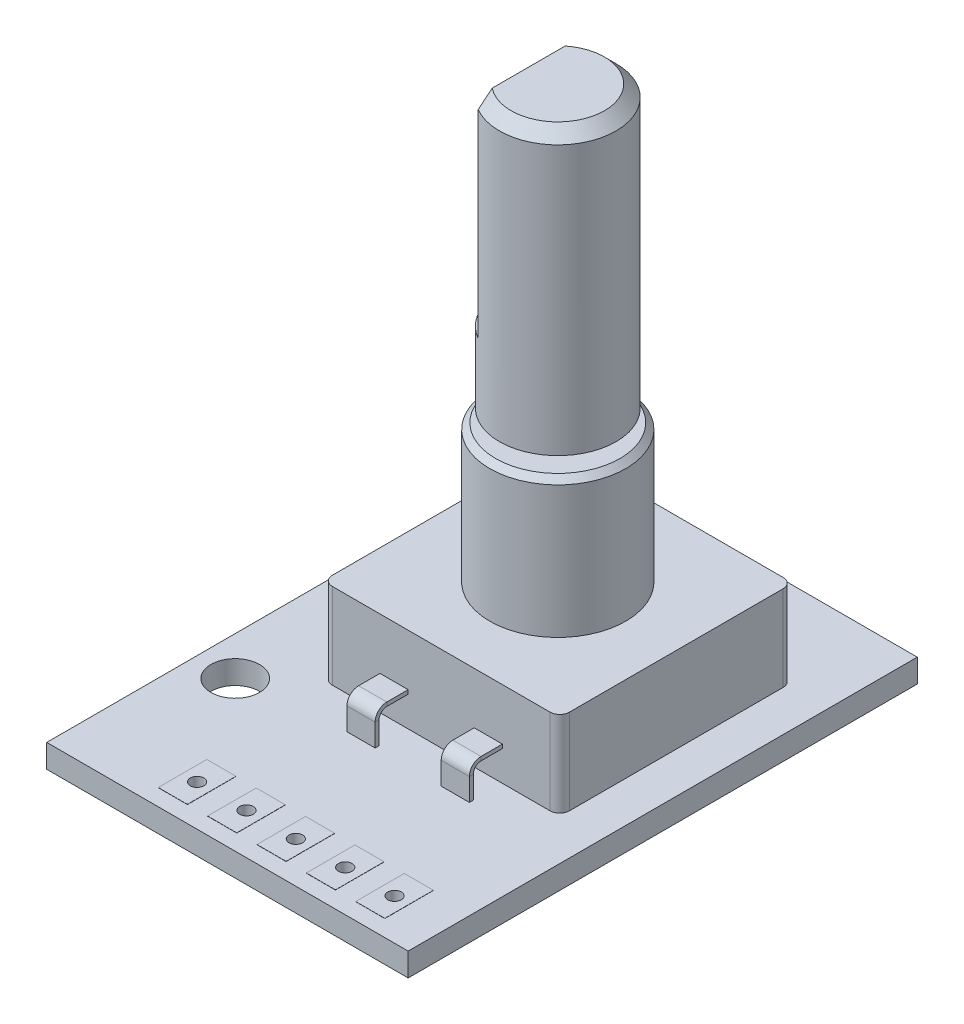
SolidWorks part; units mm, degrees
ref_plane "Front Plane" through (0, 0, 0) normal (0, 0, 1) x (1, 0, 0)
ref_plane "Top Plane" through (0, 0, 0) normal (0, 1, 0) x (1, 0, 0)
ref_plane "Right Plane" through (0, 0, 0) normal (1, 0, 0) x (0, 0, -1)
sketch "Sketch1" plane through (0, 0, 0) normal (0, 1, 0) x (1, 0, 0)
  line L0 (-7.3, 8.3) -> (-7.3, -5.4) construction
  line L1 (-9.3, 13.1) -> (9.3, 13.1)
  line L2 (-9.3, 13.1) -> (-9.3, -13.1)
  line L3 (-9.3, -13.1) -> (9.3, -13.1)
  line L4 (9.3, 13.1) -> (9.3, -13.1)
  line L5 (-9.3, 13.1) -> (9.3, -13.1) construction
  line L6 (-9.3, -13.1) -> (9.3, 13.1) construction
  circle A0 centre (-7.3, 8.3) radius 1.25
  circle A1 centre (-7.3, -5.4) radius 1.25
  point P0 (0, 0)
  point P11 (0, 0)
  point P12 (0, 0)
  point P13 (-6.0699, 9.8258)
  dimension "D3" = 2.5
  dimension "D1" = 18.6
  dimension "D2" = 26.2
  dimension "D4" = 13.7
  dimension "D5" = 4.8
  dimension "D6" = 2
extrude "Boss-Extrude1" add sketch "Sketch1" along normal blind 1.2
sketch "Sketch3" plane through (0, 1.2, 0) normal (0, 1, 0) x (1, 0, 0)
  line L0 (9.3, -13.1) -> (9.3, 13.1) construction
  line L1 (-5, -3.2) -> (7.2, -3.2)
  line L2 (-5, -3.2) -> (-5, 8.8)
  line L3 (-5, 8.8) -> (7.2, 8.8)
  line L4 (7.2, -3.2) -> (7.2, 8.8)
  line L5 (-5, -3.2) -> (7.2, 8.8) construction
  line L6 (-5, 8.8) -> (7.2, -3.2) construction
  line L7 (9.3, 13.1) -> (-9.3, 13.1) construction
  point P0 (1.1, 2.8)
  dimension "D1" = 12
  dimension "D2" = 12.2
  dimension "D3" = 2.1
  dimension "D4" = 4.3
extrude "Boss-Extrude2" add sketch "Sketch3" along normal blind 4.4
sketch3d "3DSketch5"
  line L0 (1.1, 5.6, 3.2) -> (1.1, 1.2, 3.2) construction
  line L7 (-5, 5.6, 3.2) -> (7.2, 5.6, 3.2) construction
  line L8 (-5, 1.2, 3.2) -> (7.2, 1.2, 3.2) construction
  line L9 (-1.325, 2.85, 3.2) -> (-1.325, 2.85, 4.3)
  line L10 (-1.325, 2.35, 4.8) -> (-1.325, 1.2, 4.8)
  arc A0 (-1.325, 2.85, 4.3) -> (-1.325, 2.35, 4.8) centre (-1.325, 2.35, 4.3) ccw
  point P0 (-1.325, 2.85, 3.2)
  point P1 (0, 0, 0)
  point P2 (0, 0, 0)
  point P14 (0, 0, 0)
  point P15 (-1.325, 2.85, 4.8)
  point P16 (-0.825, 2.35, 4.3)
  dimension "D3" = 0.5
  dimension "D1" = 2.425
  dimension "D2" = 1.65
  dimension "D5" = 1.6
sketch "Sketch10" plane through (0, 0, 3.2) normal (0, 0, 1) x (1, 0, 0)
  line L1 (-2.05, 2.75) -> (-0.6, 2.75)
  line L2 (-2.05, 2.75) -> (-2.05, 2.95)
  line L3 (-2.05, 2.95) -> (-0.6, 2.95)
  line L4 (-0.6, 2.75) -> (-0.6, 2.95)
  line L5 (-2.05, 2.75) -> (-0.6, 2.95) construction
  line L6 (-2.05, 2.95) -> (-0.6, 2.75) construction
  point P0 (-1.325, 2.85)
  dimension "D1" = 1.45
  dimension "D2" = 0.2
sweep "Sweep3" add profiles "Sketch10" path "3DSketch5"
ref_plane "Plane4" through (1.1, 0, 0) normal (-1, 0, 0) x (0, 0, 1)
mirror "Mirror2" about plane through (1.1, 0, 0) normal (-1, 0, 0) of "Sweep3"
sketch "Sketch13" plane through (0, 0, -8.8) normal (0, 0, -1) x (-1, 0, 0)
  line L0 (-1.1, 5.6) -> (-1.1, 1.2) construction
  line L1 (-1.825, 2.7) -> (-0.375, 2.7)
  line L2 (-1.825, 2.7) -> (-1.825, 2.9)
  line L3 (-1.825, 2.9) -> (-0.375, 2.9)
  line L4 (-0.375, 2.7) -> (-0.375, 2.9)
  line L5 (-1.825, 2.7) -> (-0.375, 2.9) construction
  line L6 (-1.825, 2.9) -> (-0.375, 2.7) construction
  line L7 (-7.2, 5.6) -> (5, 5.6) construction
  line L8 (-7.2, 1.2) -> (5, 1.2) construction
  point P0 (-1.1, 2.8)
  dimension "D1" = 1.45
  dimension "D2" = 0.2
  dimension "D5" = 1.6
sketch3d "3DSketch6"
  line L2 (1.1, 2.8, -8.8) -> (1.1, 2.8, -9.75)
  line L6 (1.1, 2.3, -10.25) -> (1.1, 1.2, -10.25)
  arc A0 (1.1, 2.8, -9.75) -> (1.1, 2.3, -10.25) centre (1.1, 2.3, -9.75) ccw
  point P2 (1.1, 2.8, -10.25)
  point P5 (0.6, 2.3, -9.75)
  point P14 (0, 0, 0)
  point P15 (0, 0, 0)
  dimension "D2" = 0.5
  dimension "D1" = 1.45
sweep "Sweep4" add profiles "Sketch13" path "3DSketch6"
pattern_linear "LPattern1" count 2 spacing 2.85 along (-1, 0, 0) of "Sweep4"
pattern_linear "LPattern2" count 2 spacing 2.85 along (1, 0, 0) of "Sweep4"
sketch "Sketch14" plane through (0, 5.6, 0) normal (0, 1, 0) x (1, 0, 0)
  line L0 (-5, 8.8) -> (7.2, -3.2) construction
  line L1 (-5, -3.2) -> (7.2, 8.8) construction
  circle A0 centre (1.1, 2.8) radius 3.5
  dimension "D1" = 7
extrude "Boss-Extrude4" add sketch "Sketch14" along normal blind 7.1
chamfer "Chamfer1" distance 0.3 angle 45 1 edges at (1.1, 12.7, 0.7)
sketch "Sketch15" plane through (0, 12.7, 0) normal (0, 1, 0) x (1, 0, 0)
  circle A2 centre (1.1, 2.8) radius 1.9
  circle A3 centre (1.1, 2.8) radius 1.9
  dimension "D1" = 1.3
extrude "Boss-Extrude5" add sketch "Sketch15" along normal blind 0.65
sketch "Sketch16" plane through (0, 13.35, 0) normal (0, 1, 0) x (1, 0, 0)
  circle A0 centre (1.1, 2.8) radius 3
  dimension "D1" = 6
extrude "Boss-Extrude6" add sketch "Sketch16" along normal blind 14.45
chamfer "Chamfer2" distance 0.6 angle 45 1 edges at (1.1, 27.8, 0.2)
sketch "Sketch17" plane through (0, 27.8, 0) normal (0, 1, 0) x (1, 0, 0)
  line L0 (-0.3967, 5.4) -> (-0.3967, 0.2)
  circle A1 centre (1.1, 2.8) radius 3
  arc A2 (-0.3967, 5.4) -> (-0.3967, 0.2) centre (1.1, 2.8) ccw
  dimension "D2" = 5.2
  dimension "D1" = 0
extrude "Cut-Extrude1" cut sketch "Sketch17" against normal blind 10.8
sketch "Sketch18" plane through (0, 1.2, 0) normal (0, 1, 0) x (1, 0, 0)
  line L0 (-9.3, -13.1) -> (9.3, -13.1) construction
  line L1 (9.3, -13.1) -> (9.3, 13.1) construction
  circle A0 centre (6.5, -11) radius 0.35
  circle A1 centre (3.96, -11) radius 0.35
  circle A2 centre (1.42, -11) radius 0.35
  circle A3 centre (-1.12, -11) radius 0.35
  circle A4 centre (-3.66, -11) radius 0.35
  dimension "D1" = 0.7
  dimension "D2" = 2.1
  dimension "D3" = 2.8
  dimension "D4" = 5
extrude "Cut-Extrude2" cut sketch "Sketch18" against normal up to surface (1.2 mm away) up to face at (0, 0, 0)
sketch "Sketch19" plane through (0, 1.2, 0) normal (0, 1, 0) x (1, 0, 0)
  line L0 (4.71, -12.25) -> (4.71, -9.75)
  line L1 (5.75, -12.25) -> (7.25, -12.25)
  line L2 (5.75, -12.25) -> (5.75, -9.75)
  line L3 (5.75, -9.75) -> (7.25, -9.75)
  line L4 (7.25, -12.25) -> (7.25, -9.75)
  line L5 (5.75, -12.25) -> (7.25, -9.75) construction
  line L6 (5.75, -9.75) -> (7.25, -12.25) construction
  line L7 (3.21, -9.75) -> (4.71, -9.75)
  line L8 (3.21, -12.25) -> (3.21, -9.75)
  line L9 (3.21, -12.25) -> (4.71, -12.25)
  line L10 (2.17, -12.25) -> (2.17, -9.75)
  line L11 (0.67, -9.75) -> (2.17, -9.75)
  line L12 (0.67, -12.25) -> (0.67, -9.75)
  line L13 (0.67, -12.25) -> (2.17, -12.25)
  line L14 (-0.37, -12.25) -> (-0.37, -9.75)
  line L15 (-1.87, -9.75) -> (-0.37, -9.75)
  line L16 (-1.87, -12.25) -> (-1.87, -9.75)
  line L17 (-1.87, -12.25) -> (-0.37, -12.25)
  line L18 (-2.91, -12.25) -> (-2.91, -9.75)
  line L19 (-4.41, -9.75) -> (-2.91, -9.75)
  line L20 (-4.41, -12.25) -> (-4.41, -9.75)
  line L21 (-4.41, -12.25) -> (-2.91, -12.25)
  circle A0 centre (6.5, -11) radius 0.35
  circle A1 centre (3.96, -11) radius 0.35
  circle A2 centre (1.42, -11) radius 0.35
  circle A3 centre (-1.12, -11) radius 0.35
  circle A4 centre (-3.66, -11) radius 0.35
  point P0 (6.5, -11)
  dimension "D3" = 5
  dimension "D1" = 2.5
  dimension "D2" = 1.5
extrude "Boss-Extrude7" add sketch "Sketch19" along normal blind 0.01
ref_plane "Plane5" through (0, 0.6, 0) normal (0, 1, 0) x (1, 0, 0)
mirror "Mirror3" about plane through (0, 0.6, 0) normal (0, 1, 0) of "Boss-Extrude7"
fillet "Fillet1" radius 0.5 4 edges at (-5, 3.4, -8.8) (-5, 3.4, 3.2) (7.2, 3.4, 3.2) (7.2, 3.4, -8.8)
